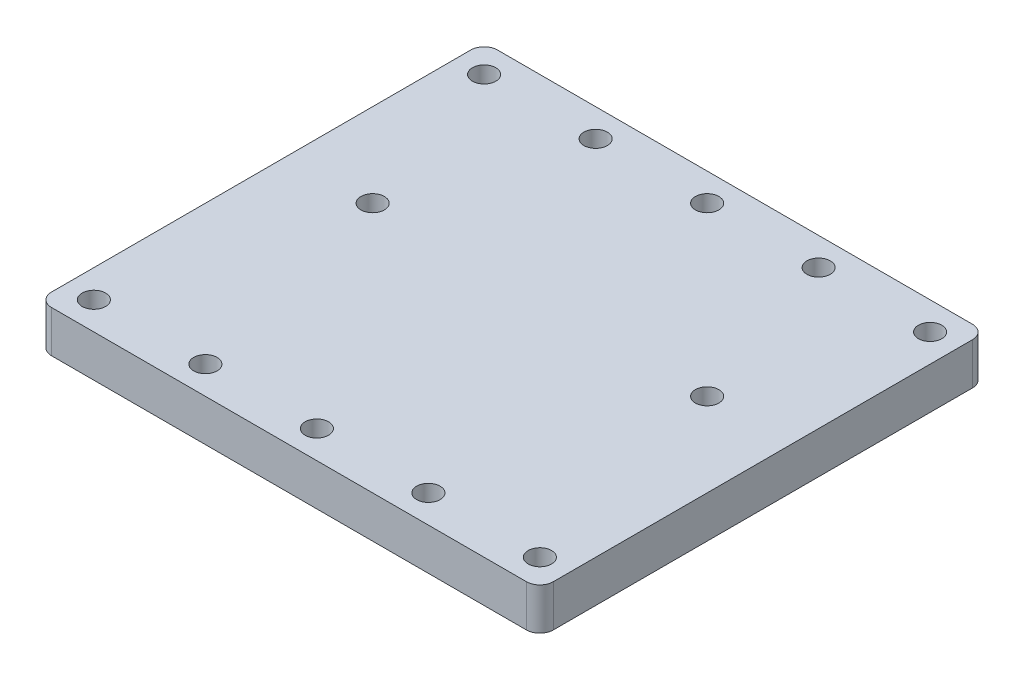
SolidWorks part; units mm, degrees
ref_plane "Front Plane" through (0, 0, 0) normal (0, 0, 1) x (1, 0, 0)
ref_plane "Top Plane" through (0, 0, 0) normal (0, 1, 0) x (1, 0, 0)
ref_plane "Right Plane" through (0, 0, 0) normal (1, 0, 0) x (0, 0, -1)
sketch "Sketch1" plane through (0, 0, 0) normal (0, 1, 0) x (1, 0, 0)
  line L1 (57.15, 50.8) -> (-57.15, 50.8)
  line L2 (57.15, 50.8) -> (57.15, -50.8)
  line L3 (57.15, -50.8) -> (-57.15, -50.8)
  line L4 (-57.15, 50.8) -> (-57.15, -50.8)
  line L5 (57.15, 50.8) -> (-57.15, -50.8) construction
  line L6 (57.15, -50.8) -> (-57.15, 50.8) construction
  point P0 (0, 0)
extrude "Boss-Extrude1" add sketch "Sketch1" along normal blind 9.525
fillet "Fillet1" radius 3.048 4 edges at (-57.15, 4.7625, -50.8) (57.15, 4.7625, -50.8) (57.15, 4.7625, 50.8) (-57.15, 4.7625, 50.8)
sketch "Sketch3" plane through (0, 9.525, 0) normal (0, 1, 0) x (1, 0, 0)
  line L2 (57.15, 47.752) -> (50.8, 47.752)
  line L3 (50.8, 50.8) -> (50.8, 44.45)
  line L4 (54.102, 50.8) -> (-54.102, 50.8) construction
  circle A0 centre (50.8, 44.45) radius 2.667
  circle A1 centre (25.4, 44.45) radius 2.667
  circle A2 centre (0, 44.45) radius 2.667
  circle A3 centre (-25.4, 44.45) radius 2.667
  circle A4 centre (-50.8, 44.45) radius 2.667
  circle A5 centre (25.4, -44.45) radius 2.667
  circle A6 centre (0, -44.45) radius 2.667
  circle A7 centre (-25.4, -44.45) radius 2.667
  circle A8 centre (-50.8, -44.45) radius 2.667
  circle A9 centre (50.8, -44.45) radius 2.667
  circle A10 centre (38.1, 44.45) radius 2.667
  circle A11 centre (-38.1, 44.45) radius 2.667
  circle A12 centre (38.1, 6.35) radius 2.667
  circle A13 centre (-38.1, 6.35) radius 2.667
  circle A14 centre (50.8, 6.35) radius 2.667
  circle A15 centre (-25.4, 6.35) radius 2.667
  dimension "D1" = 5
  dimension "D2" = 2
  dimension "D3" = 2
  dimension "D4" = 2
extrude "Cut-Extrude1" cut sketch "Sketch3" against normal up to surface (9.525 mm away)
